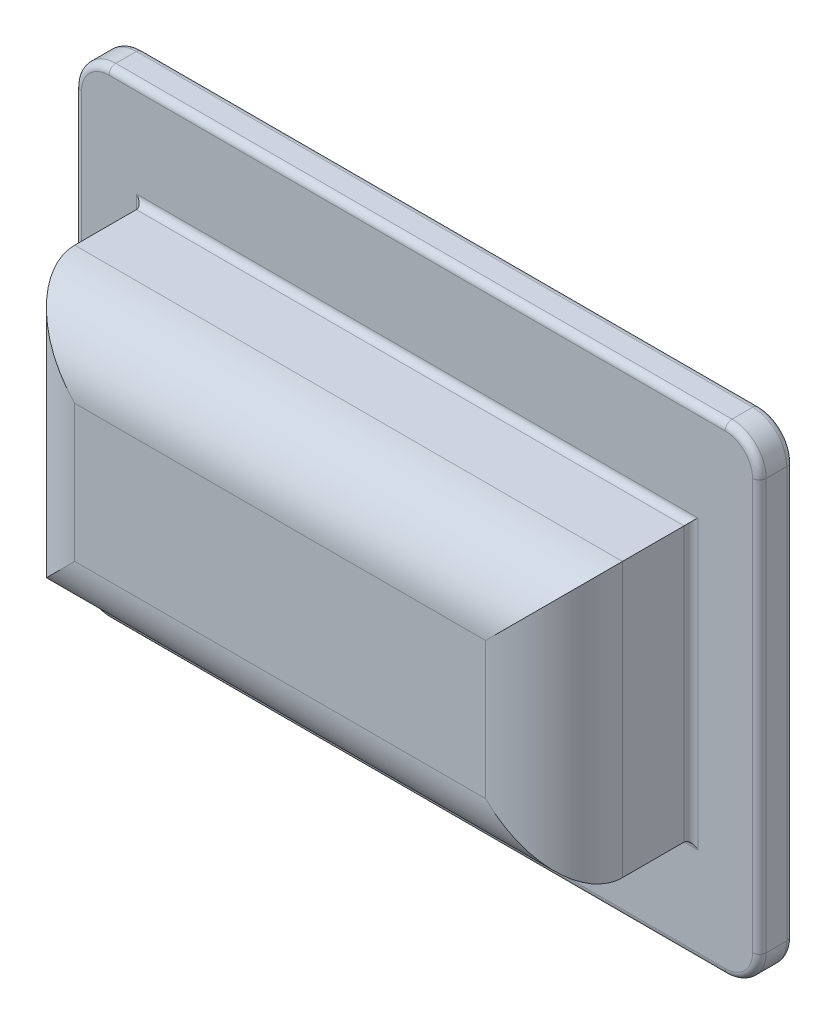
SolidWorks part; units mm, degrees
ref_plane "Front Plane" through (0, 0, 0) normal (0, 0, 1) x (1, 0, 0)
ref_plane "Top Plane" through (0, 0, 0) normal (0, 1, 0) x (1, 0, 0)
ref_plane "Right Plane" through (0, 0, 0) normal (1, 0, 0) x (0, 0, -1)
sketch "Sketch1" plane through (0, 0, 0) normal (0, 0, 1) x (1, 0, 0)
  line L1 (-20, -10) -> (20, -10)
  line L2 (-20, -10) -> (-20, 10)
  line L3 (-20, 10) -> (20, 10)
  line L4 (20, -10) -> (20, 10)
  line L5 (-20, -10) -> (20, 10) construction
  line L6 (-20, 10) -> (20, -10) construction
  point P0 (0, 0)
  dimension "D1" = 20
  dimension "D2" = 40
extrude "Boss-Extrude1" add sketch "Sketch1" along normal blind 10
sketch "Sketch2" plane through (0, 0, 0) normal (0, 0, 1) x (1, 0, 0)
  line L1 (-16, -6) -> (16, -6)
  line L2 (-16, -6) -> (-16, 6)
  line L3 (-16, 6) -> (16, 6)
  line L4 (16, -6) -> (16, 6)
  line L5 (-16, -6) -> (16, 6) construction
  line L6 (-16, 6) -> (16, -6) construction
  point P0 (0, 0)
  dimension "D1" = 32
  dimension "D2" = 12
extrude "Cut-Extrude1" cut sketch "Sketch2" along normal blind 5
fillet "Fillet1" radius 5 4 edges at (0, -10, 10) (-20, 0, 10) (0, 10, 10) (20, 0, 10)
sketch "Sketch3" plane through (0, 0, 0) normal (0, 0, 1) x (1, 0, 0)
  line L0 (20, 10) -> (-20, 10) construction
  line L1 (-25, -15) -> (25, -15) construction
  line L2 (-25, -15) -> (-25, 15) construction
  line L3 (-25, 15) -> (25, 15) construction
  line L4 (25, -15) -> (25, 15) construction
  line L5 (-25, -15) -> (25, 15) construction
  line L6 (-25, 15) -> (25, -15) construction
  line L7 (20, -10) -> (20, 10) construction
  line L8 (0, 0) -> (0, 15) construction
  line L9 (0, 0) -> (25, 0) construction
  line L10 (22.5, 17.5) -> (-22.5, 17.5)
  line L11 (25, 15) -> (25, -15)
  line L12 (-25, 15) -> (-25, -15)
  line L13 (22.5, -17.5) -> (-22.5, -17.5)
  line L15 (-16, -6) -> (16, -6)
  line L16 (-16, -6) -> (-16, 6)
  line L17 (-16, 6) -> (16, 6)
  line L18 (16, -6) -> (16, 6)
  line L19 (-16, -6) -> (16, 6) construction
  line L20 (-16, 6) -> (16, -6) construction
  arc A0 (25, 15) -> (22.5, 17.5) centre (22.5, 15) ccw
  arc A1 (-22.5, 17.5) -> (-25, 15) centre (-22.5, 15) ccw
  arc A2 (-22.5, -17.5) -> (-25, -15) centre (-22.5, -15) cw
  arc A3 (25, -15) -> (22.5, -17.5) centre (22.5, -15) cw
  point P0 (0, 0)
  point P15 (0, 17.5)
  dimension "D1" = 5
  dimension "D2" = 5
  dimension "D3" = 2.5
extrude "Boss-Extrude2" add sketch "Sketch3" against normal blind 2.5
fillet "Fillet2" radius 1 4 edges at (0, 6, 5) (-16, 0, 5) (0, -6, 5) (16, 0, 5)
fillet "Fillet3" radius 2 4 edges at (16, 0, -2.5) (0, -6, -2.5) (-16, 0, -2.5) (0, 6, -2.5)
fillet "SmoothingFillet" radius 0.5 20 edges at (-24.2678, -16.7678, 0) (-25, 0, 0) (-24.2678, 16.7678, 0) (0, 17.5, 0) (24.2678, 16.7678, 0) (25, 0, 0) (24.2678, -16.7678, 0) (-24.2678, -16.7678, -2.5) (-25, 0, -2.5) (-24.2678, 16.7678, -2.5) (0, 17.5, -2.5) (24.2678, 16.7678, -2.5) (25, 0, -2.5) (24.2678, -16.7678, -2.5) (0, -10, 0) (0, -17.5, 0) (0, -17.5, -2.5) (20, 0, 0) (0, 10, 0) (-20, 0, 0)
equation "\"ChamberLength\"= 30mm"
equation "\"ChamberWIdth\"= 10mm"
equation "\"D1@Sketch1\"=\"ChamberWIdth\"+10"
equation "\"D2@Sketch1\"=\"ChamberLength\"+10"
equation "\"D1@Sketch2\"=\"ChamberLength\"+2"
equation "\"D2@Sketch2\"=\"ChamberWIdth\"+2"
equation "\"SmoothingRadius\"= .5mm"
equation "\"D1@SmoothingFillet\"=\"SmoothingRadius\""
